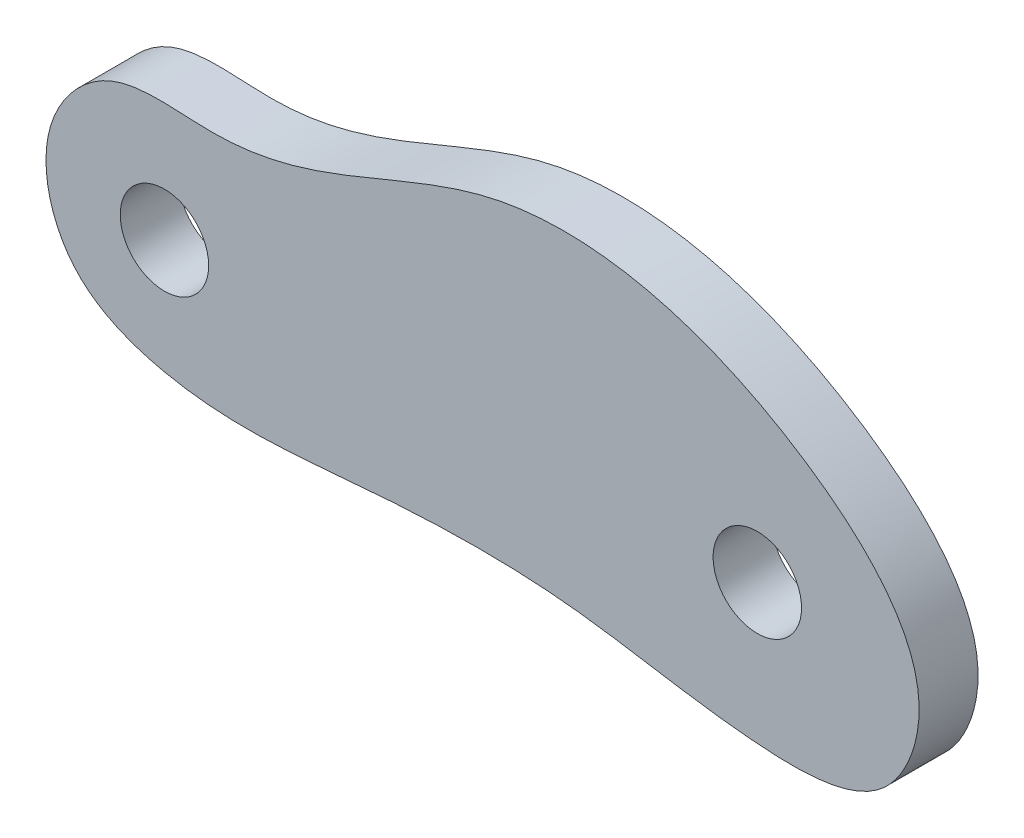
SolidWorks part; units mm, degrees
ref_plane "Front Plane" through (0, 0, 0) normal (0, 0, 1) x (1, 0, 0)
ref_plane "Top Plane" through (0, 0, 0) normal (0, 1, 0) x (1, 0, 0)
ref_plane "Right Plane" through (0, 0, 0) normal (1, 0, 0) x (0, 0, -1)
sketch "Sketch1" plane through (0, 0, 0) normal (0, 0, 1) x (1, 0, 0)
  line L0 (302.5, 350) -> (1512.5, 350) construction
  circle A0 centre (288.5908, 226.8062) radius 2.3813
  circle A1 centre (256.6563, 226.8062) radius 2.3813
  spline S0 degree 3 poles (267.6484, 220.8463) (258.6563, 219.6106) (251.0135, 222.496) (249.4339, 228.8917) (253.6892, 233.8257) (258.8208, 232.8518) (265.7966, 233.9192) (275.5843, 239.7662) (289.392, 236.4389) (298.8336, 227.3806) (295.5374, 219.1612) (287.1502, 219.054) (278.5271, 221.0945) (267.6484, 220.8463) (258.6563, 219.6106) (251.0135, 222.496) knots -0.292758 -0.199814 -0.103029 0 0.048868 0.104914 0.150292 0.201901 0.236562 0.344194 0.499123 0.600927 0.643564 0.707242 0.800186 0.896971 1 1.048868 1.104914 1.150292 only from (256.6563, 220.6584) to (256.6563, 220.6584)
  dimension "D24" = 4.7625
  dimension "D25" = 4.7625
  dimension "D1" = 250.5085
  dimension "D2" = 251.8747
  dimension "D3" = 253.7532
  dimension "D4" = 256.6563
  dimension "D5" = 259.3887
  dimension "D6" = 263.1457
  dimension "D7" = 267.9273
  dimension "D8" = 274.2459
  dimension "D9" = 278.5152
  dimension "D10" = 288.5908
  dimension "D11" = 290.8108
  dimension "D12" = 295.4217
  dimension "D13" = 297.3002
  dimension "D14" = 219.2922
  dimension "D15" = 220.6584
  dimension "D16" = 223.0492
  dimension "D17" = 224.9277
  dimension "D18" = 229.0262
  dimension "D19" = 232.7832
  dimension "D20" = 233.1248
  dimension "D21" = 233.6371
  dimension "D22" = 233.9786
  dimension "D23" = 237.5649
extrude "Boss-Extrude1" add sketch "Sketch1" along normal blind 3.175
